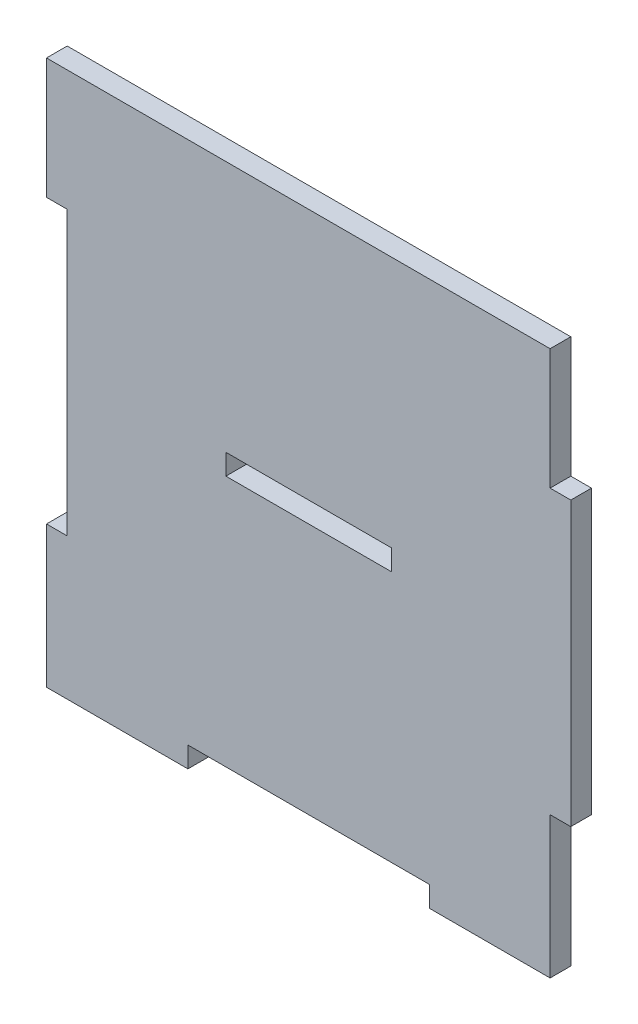
SolidWorks part; units mm, degrees
ref_plane "Front Plane" through (0, 0, 0) normal (0, 0, 1) x (1, 0, 0)
ref_plane "Top Plane" through (0, 0, 0) normal (0, 1, 0) x (1, 0, 0)
ref_plane "Right Plane" through (0, 0, 0) normal (1, 0, 0) x (0, 0, -1)
sketch "Sketch1" plane through (0, 0, 0) normal (0, 0, 1) x (1, 0, 0)
  line L0 (0, 35) -> (0, -38) construction
  line L5 (-35, 38) -> (-17.5, 38)
  line L6 (-35, 20.5) -> (-35, -20.5)
  line L7 (-17.5, -38) -> (17.5, -38)
  line L24 (35, 38) -> (35, 20.5)
  line L25 (-35, 38) -> (35, -38) construction
  line L26 (-35, -38) -> (35, 38) construction
  line L27 (-35, 0) -> (35, 0) construction
  line L31 (-35, -20.5) -> (-38, -20.5)
  line L32 (-35, 20.5) -> (-38, 20.5)
  line L33 (-38, 20.5) -> (-38, 38)
  line L34 (-38, 38) -> (-35, 38)
  line L35 (-38, -20.5) -> (-38, -38)
  line L36 (-17.5, 38) -> (17.5, 38)
  line L37 (35, -38) -> (35, -41)
  line L38 (35, -20.5) -> (38, -20.5)
  line L39 (35, -41) -> (17.5, -41)
  line L40 (35, 20.5) -> (38, 20.5)
  line L41 (17.5, -41) -> (17.5, -38)
  line L42 (-17.5, -38) -> (-17.5, -41)
  line L43 (38, 20.5) -> (38, -20.5)
  line L45 (-35, -41) -> (-17.5, -41)
  line L46 (17.5, 38) -> (35, 38)
  line L47 (35, -20.5) -> (35, -38)
  line L48 (-38, -38) -> (-38, -41)
  line L49 (-38, -41) -> (-35, -41)
  point P0 (0, 0)
  dimension "D1" = 76
  dimension "D2" = 70
  dimension "D3" = 17.5
  dimension "D4" = 17.5
  dimension "D5" = 3
  dimension "D6" = 3
  dimension "D7" = 3
extrude "Boss-Extrude1" add sketch "Sketch1" along normal blind 3
sketch "Sketch2" plane through (0, 0, 3) normal (0, 0, 1) x (1, 0, 0)
  line L1 (-12, -1.5) -> (12, -1.5)
  line L2 (-12, -1.5) -> (-12, 1.5)
  line L3 (-12, 1.5) -> (12, 1.5)
  line L4 (12, -1.5) -> (12, 1.5)
  line L5 (-12, -1.5) -> (12, 1.5) construction
  line L6 (-12, 1.5) -> (12, -1.5) construction
  point P0 (0, 0)
  dimension "D1" = 24
  dimension "D2" = 3
extrude "Cut-Extrude1" cut sketch "Sketch2" against normal blind 3
